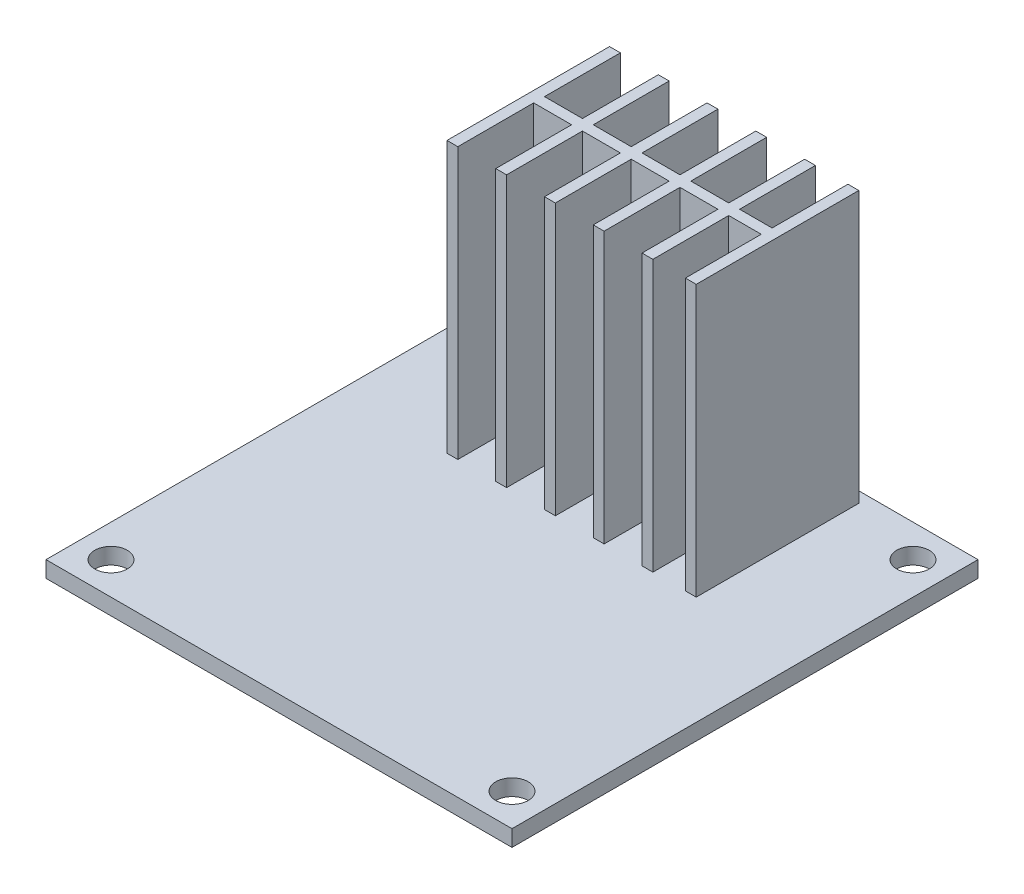
SolidWorks part; units mm, degrees
ref_plane "Front Plane" through (0, 0, 0) normal (0, 0, 1) x (1, 0, 0)
ref_plane "Top Plane" through (0, 0, 0) normal (0, 1, 0) x (1, 0, 0)
ref_plane "Right Plane" through (0, 0, 0) normal (1, 0, 0) x (0, 0, -1)
sketch "Sketch1" plane through (0, 0, 0) normal (0, 1, 0) x (1, 0, 0)
  line L1 (-21.5, -21.5) -> (21.5, -21.5)
  line L2 (-21.5, -21.5) -> (-21.5, 21.5)
  line L3 (-21.5, 21.5) -> (21.5, 21.5)
  line L4 (21.5, -21.5) -> (21.5, 21.5)
  line L5 (-21.5, -21.5) -> (21.5, 21.5) construction
  line L6 (-21.5, 21.5) -> (21.5, -21.5) construction
  point P0 (0, 0)
  dimension "D1" = 43
  dimension "D2" = 43
extrude "Boss-Extrude1" add sketch "Sketch1" along normal blind 1.5
sketch "Sketch2" plane through (0, 1.5, 0) normal (0, 1, 0) x (1, 0, 0)
  line L4 (21.5, -21.5) -> (21.5, 21.5)
  line L5 (21.5, 21.5) -> (-21.5, 21.5)
  line L6 (-21.5, 21.5) -> (-21.5, -21.5)
  line L7 (-21.5, -21.5) -> (21.5, -21.5)
  line L8 (21.5, -21.5) -> (21.5, 21.5)
  line L9 (21.5, 21.5) -> (-21.5, 21.5)
  line L10 (-21.5, 21.5) -> (-21.5, -21.5)
  line L11 (-21.5, -21.5) -> (21.5, -21.5)
  circle A0 centre (-18.5, 18.5) radius 1.5
  circle A2 centre (18.5, 18.5) radius 1.5
  circle A3 centre (18.5, -18.5) radius 1.5
  circle A4 centre (-18.5, -18.5) radius 1.5
  point P16 (0, 0)
  dimension "D2" = 3
  dimension "D3" = 18.5
  dimension "D4" = 18.5
  dimension "D1" = 0
  dimension "D5" = 4
extrude "Cut-Extrude1" cut sketch "Sketch2" against normal through all contours A0 | A2 | A3 | A4
sketch "Sketch3" plane through (0, 1.5, 0) normal (0, 1, 0) x (1, 0, 0)
  line L0 (-10.5, 5.5) -> (-10.5, 12.5)
  line L1 (-11.5, 5.5) -> (-10.5, 5.5)
  line L2 (-11.5, 5.5) -> (-11.5, 20.5)
  line L3 (-11.5, 20.5) -> (-10.5, 20.5)
  line L4 (21.5, -21.5) -> (21.5, 21.5)
  line L5 (21.5, 21.5) -> (-21.5, 21.5)
  line L6 (-21.5, 21.5) -> (-21.5, -21.5)
  line L7 (-21.5, -21.5) -> (21.5, -21.5)
  line L8 (21.5, -21.5) -> (21.5, 21.5)
  line L9 (21.5, 21.5) -> (-21.5, 21.5)
  line L10 (-21.5, 21.5) -> (-21.5, -21.5)
  line L11 (-21.5, -21.5) -> (21.5, -21.5)
  line L12 (11.5, 5.5) -> (11.5, 20.5)
  line L13 (-10.5, 13.5) -> (-10.5, 20.5)
  line L14 (-10.5, 6.5) -> (-10.5, 19.5) construction
  line L15 (-10.5, 12.5) -> (-7, 12.5)
  line L16 (-11.5, 12.5) -> (-11.5, 13.5)
  line L17 (-10.5, 13.5) -> (-7, 13.5)
  line L18 (11.5, 12.5) -> (11.5, 13.5)
  line L19 (10.5, 13.5) -> (10.5, 20.5)
  line L20 (10.5, 6.5) -> (10.5, 19.5) construction
  line L22 (10.5, 5.5) -> (10.5, 12.5)
  line L24 (-6, 13.5) -> (-6, 20.5)
  line L25 (-7, 5.5) -> (-7, 12.5)
  line L26 (-6, 5.5) -> (-6, 12.5)
  line L27 (-1.5, 13.5) -> (-1.5, 20.5)
  line L28 (-2.5, 5.5) -> (-2.5, 12.5)
  line L29 (-1.5, 5.5) -> (-1.5, 12.5)
  line L30 (3, 13.5) -> (3, 20.5)
  line L31 (2, 5.5) -> (2, 12.5)
  line L32 (3, 5.5) -> (3, 12.5)
  line L33 (7.5, 13.5) -> (7.5, 20.5)
  line L34 (6.5, 5.5) -> (6.5, 12.5)
  line L35 (7.5, 5.5) -> (7.5, 12.5)
  line L36 (-7, 13.5) -> (-7, 20.5)
  line L37 (-2.5, 13.5) -> (-2.5, 20.5)
  line L38 (2, 13.5) -> (2, 20.5)
  line L39 (6.5, 13.5) -> (6.5, 20.5)
  line L40 (-6, 13.5) -> (-2.5, 13.5)
  line L41 (-6, 12.5) -> (-2.5, 12.5)
  line L42 (-1.5, 13.5) -> (2, 13.5)
  line L43 (-1.5, 12.5) -> (2, 12.5)
  line L44 (3, 13.5) -> (6.5, 13.5)
  line L45 (3, 12.5) -> (6.5, 12.5)
  line L46 (7.5, 13.5) -> (10.5, 13.5)
  line L47 (7.5, 12.5) -> (10.5, 12.5)
  line L48 (-10.5, 19.5) -> (10.5, 19.5) construction
  line L49 (-7, 20.5) -> (-6, 20.5)
  line L50 (-11.5, 20.5) -> (11.5, 20.5) construction
  line L51 (-2.5, 20.5) -> (-1.5, 20.5)
  line L52 (-10.5, 6.5) -> (10.5, 6.5) construction
  line L53 (2, 20.5) -> (3, 20.5)
  line L54 (6.5, 20.5) -> (7.5, 20.5)
  line L55 (10.5, 20.5) -> (11.5, 20.5)
  line L56 (10.5, 5.5) -> (11.5, 5.5)
  line L57 (-11.5, 5.5) -> (11.5, 5.5) construction
  line L58 (6.5, 5.5) -> (7.5, 5.5)
  line L59 (2, 5.5) -> (3, 5.5)
  line L60 (-2.5, 5.5) -> (-1.5, 5.5)
  line L61 (-7, 5.5) -> (-6, 5.5)
  point P2 (0, 13)
  point P9 (0, 13)
  dimension "D2" = 1
  dimension "D3" = 15
  dimension "D4" = 23
  dimension "D5" = 0
  dimension "D6" = 1
  dimension "D1" = 0
  dimension "D7" = 1
  dimension "D8" = 5
extrude "Boss-Extrude2" add sketch "Sketch3" along normal blind 25 contours L25 L61 L26 L41 L28 L60 L29 L43 L31 L59 L32 L45 L34 L58 L35 L47 L22 L56 L12 L55 L19 L46 L33 L54 L39 L44 L30 L53 L38 L42 L27 L51 L37 L40 L24 L49 L36 L17 L13 L3 L2 L1 L0 L15
